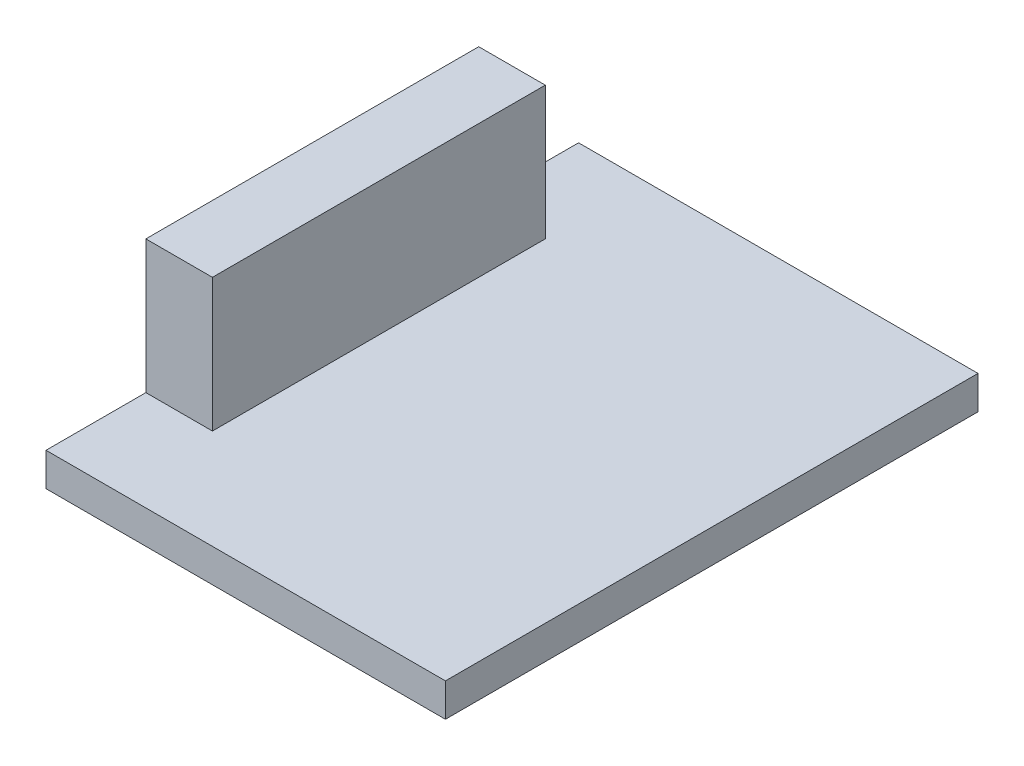
SolidWorks part; units mm, degrees
ref_plane "Front Plane" through (0, 0, 0) normal (0, 0, 1) x (1, 0, 0)
ref_plane "Top Plane" through (0, 0, 0) normal (0, 1, 0) x (1, 0, 0)
ref_plane "Right Plane" through (0, 0, 0) normal (1, 0, 0) x (0, 0, -1)
sketch "Sketch1" plane through (0, 0, 0) normal (0, 1, 0) x (1, 0, 0)
  line L1 (0, 0) -> (19.05, 0)
  line L2 (0, 0) -> (0, 25.4)
  line L3 (0, 25.4) -> (19.05, 25.4)
  line L4 (19.05, 0) -> (19.05, 25.4)
  dimension "D1" = 19.05
  dimension "D2" = 25.4
extrude "Boss-Extrude1" add sketch "Sketch1" along normal blind 1.5875
sketch "Sketch2" plane through (0, 1.5875, 0) normal (0, 1, 0) x (1, 0, 0)
  line L0 (0, 12.7) -> (19.05, 12.7) construction
  line L1 (0, 25.4) -> (0, 0) construction
  line L2 (19.05, 0) -> (19.05, 25.4) construction
  line L3 (0, 4.7625) -> (0, 20.6375)
  line L4 (0, 20.6375) -> (3.175, 20.6375)
  line L5 (3.175, 20.6375) -> (3.175, 4.7625)
  line L6 (3.175, 4.7625) -> (0, 4.7625)
  dimension "D1" = 15.875
  dimension "D2" = 3.175
extrude "Boss-Extrude2" add sketch "Sketch2" along normal blind 6.35
